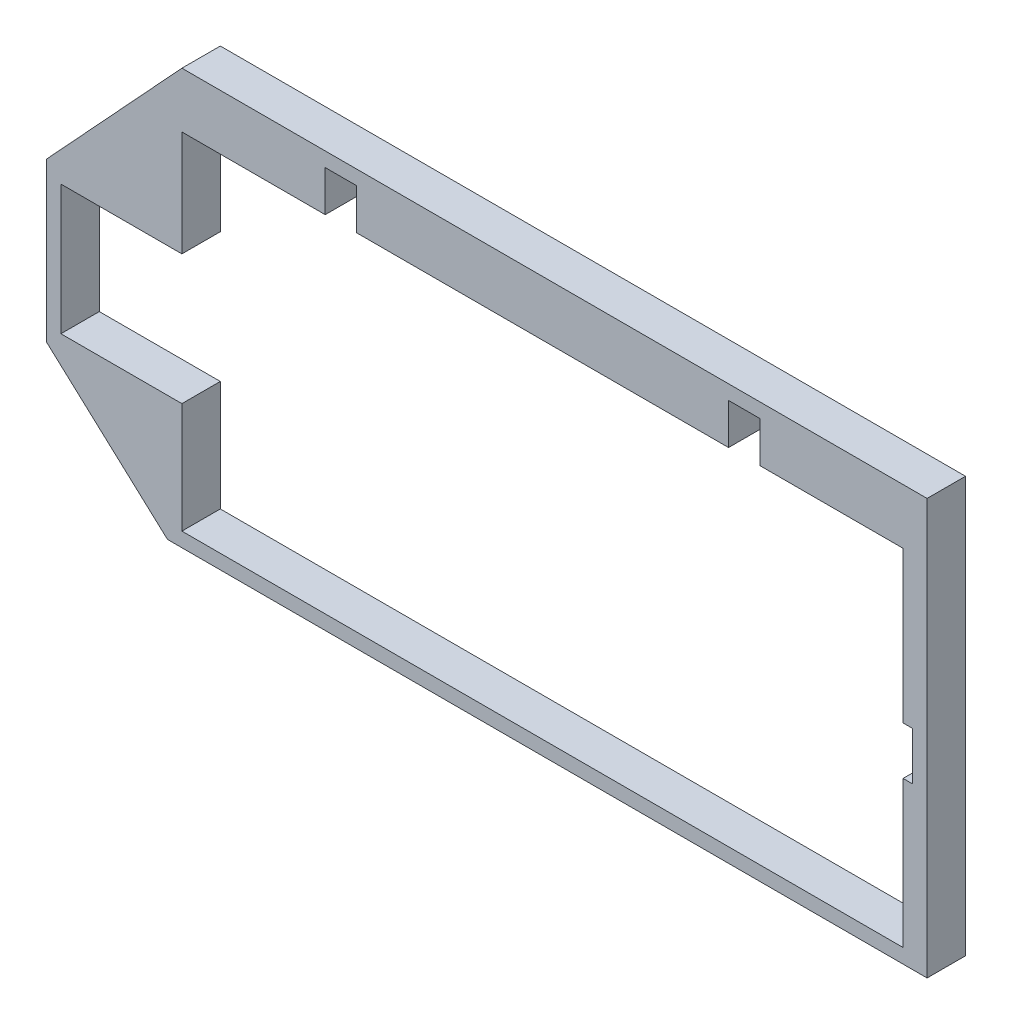
SolidWorks part; units mm, degrees
ref_plane "Front Plane" through (0, 0, 0) normal (0, 0, 1) x (1, 0, 0)
ref_plane "Top Plane" through (0, 0, 0) normal (0, 1, 0) x (1, 0, 0)
ref_plane "Right Plane" through (0, 0, 0) normal (1, 0, 0) x (0, 0, -1)
sketch "Sketch1" plane through (0, 0, 0) normal (0, 0, 1) x (1, 0, 0)
  line L0 (-150.2, 72) -> (-120.35, 72)
  line L1 (-150.2, 72) -> (-150.2, 50)
  line L2 (-150.2, 0) -> (0, 0)
  line L3 (-150.2, 23) -> (-150.2, 0)
  line L4 (-120.35, 80.5) -> (-29.85, 80.5) construction
  line L5 (-113.85, 72) -> (-113.85, 80.5)
  line L6 (-113.85, 80.5) -> (-120.35, 80.5)
  line L7 (-120.35, 72) -> (-120.35, 80.5)
  line L8 (-29.85, 72) -> (-29.85, 80.5)
  line L9 (-29.85, 80.5) -> (-36.35, 80.5)
  line L10 (-36.35, 72) -> (-36.35, 80.5)
  line L11 (-113.85, 72) -> (-36.35, 72)
  line L12 (-29.85, 72) -> (0, 72)
  line L13 (-175.4, 50) -> (0, 50) construction
  line L14 (-150.2, 50) -> (-175.4, 50)
  line L15 (-150.2, 23) -> (-175.4, 23)
  line L16 (-175.4, 50) -> (-175.4, 23)
  line L17 (0, 72) -> (0, 40.5)
  line L18 (-178.4, 53) -> (-150.2, 83.5)
  line L19 (5, -3) -> (-153.2, -3)
  line L20 (5, -3) -> (5, 83.5)
  line L22 (-178.4, 20) -> (-178.4, 53)
  line L23 (-150.2, 83.5) -> (5, 83.5)
  line L24 (-178.4, 20) -> (-153.2, -3)
  line L25 (0, 30.5) -> (0, 0)
  line L26 (0, 40.5) -> (2, 40.5)
  line L28 (0, 30.5) -> (2, 30.5)
  line L29 (2, 40.5) -> (2, 30.5)
  point P15 (-75.1, 80.5)
  point P16 (-117.1, 80.5)
  point P17 (-33.1, 80.5)
  point P18 (-75.1, 0)
  point P30 (2, 35.5)
  dimension "D1" = 72
  dimension "D2" = 6.5
  dimension "D3" = 8.5
  dimension "D4" = 25.2
  dimension "D5" = 49
  dimension "D6" = 27
  dimension "D7" = 84
  dimension "D8" = 150.2
  dimension "D9" = 3
  dimension "D10" = 3
  dimension "D11" = 3
  dimension "D12" = 3
  dimension "D13" = 3
  dimension "D14" = 3
  dimension "D15" = 3
  dimension "D16" = 10
  dimension "D17" = 36.5
  dimension "D18" = 2
extrude "Boss-Extrude1" add sketch "Sketch1" along normal blind 8
